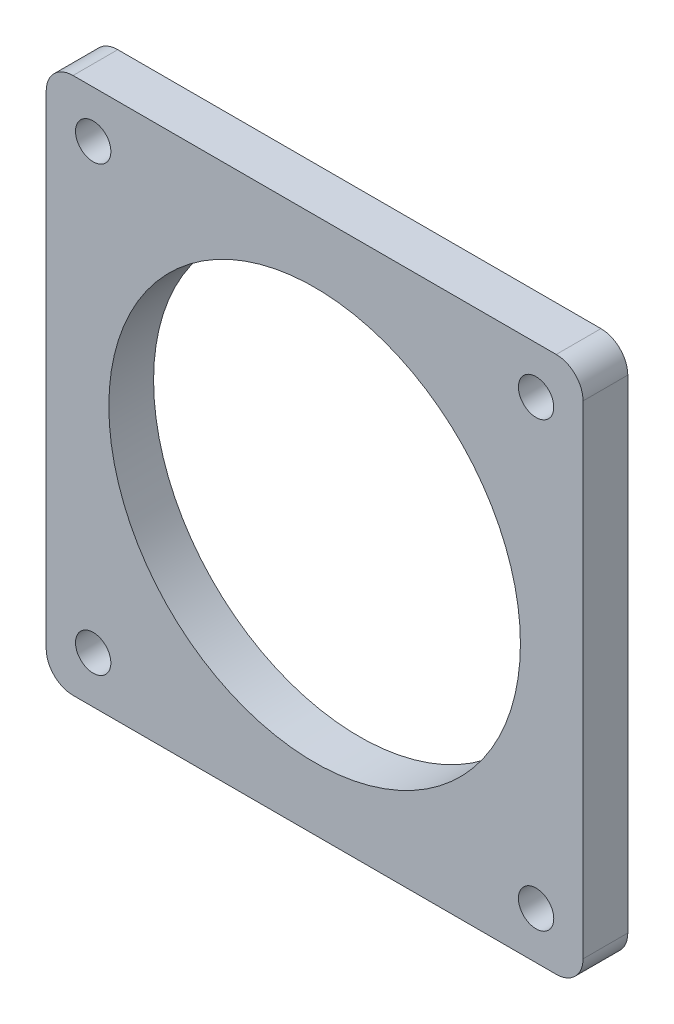
SolidWorks part; units mm, degrees
material "Glass"
ref_plane "Front Plane" through (0, 0, 0) normal (0, 0, 1) x (1, 0, 0)
ref_plane "Top Plane" through (0, 0, 0) normal (0, 1, 0) x (1, 0, 0)
ref_plane "Right Plane" through (0, 0, 0) normal (1, 0, 0) x (0, 0, -1)
sketch "Sketch1" plane through (0, 0, 0) normal (0, 0, 1) x (1, 0, 0)
  line L0 (0, 0) -> (0, 38.5966) construction
  line L1 (-27, 30) -> (27, 30)
  line L2 (-30, 27) -> (-30, -27)
  line L3 (-27, -30) -> (27, -30)
  line L4 (30, 27) -> (30, -27)
  line L5 (-30, 30) -> (30, -30) construction
  line L6 (-30, -30) -> (30, 30) construction
  line L7 (0, 0) -> (-35.9434, 0) construction
  circle A0 centre (0, 0) radius 23
  circle A1 centre (-24.75, 24.75) radius 1.975
  circle A2 centre (24.75, 24.75) radius 1.975
  circle A3 centre (24.75, -24.75) radius 1.975
  circle A4 centre (-24.75, -24.75) radius 1.975
  arc A5 (27, -30) -> (30, -27) centre (27, -27) ccw
  arc A6 (-30, -27) -> (-27, -30) centre (-27, -27) ccw
  arc A7 (27, 30) -> (30, 27) centre (27, 27) cw
  arc A8 (-27, 30) -> (-30, 27) centre (-27, 27) ccw
  point P0 (0, 0)
  dimension "D3" = 46
  dimension "D4" = 3.95
  dimension "D7" = 3
  dimension "D8" = 3
  dimension "D9" = 3
  dimension "D10" = 3
  dimension "D1" = 60
  dimension "D2" = 60
  dimension "D6" = 49.5
extrude "Boss-Extrude1" add sketch "Sketch1" along normal blind 5
